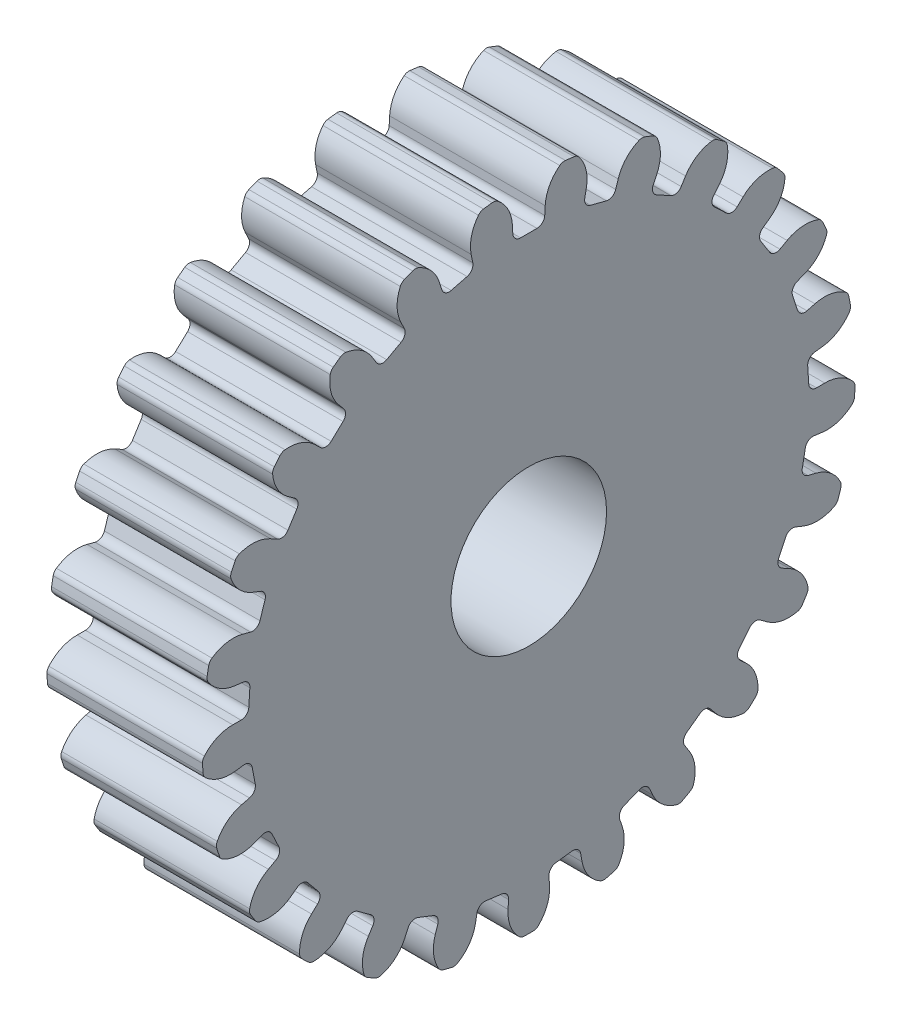
SolidWorks part; units mm, degrees
ref_plane "Plan de face" through (0, 0, 0) normal (0, 0, 1) x (1, 0, 0)
ref_plane "Plan de dessus" through (0, 0, 0) normal (0, 1, 0) x (1, 0, 0)
ref_plane "Plan de droite" through (0, 0, 0) normal (1, 0, 0) x (0, 0, -1)
sketch "Esquisse1" plane through (0, 0, 0) normal (1, 0, 0) x (0, 0, -1)
  circle A0 centre (0, 0) radius 10.5
  circle A1 centre (0, 0) radius 2.5
  dimension "D1" = 21
  dimension "D2" = 5
extrude "Extrusion1" add sketch "Esquisse1" along normal blind 5
sketch "Esquisse22" plane through (0, 0, 0) normal (-1, 0, 0) x (0, 0, 1)
  line L0 (0, 0) -> (0, 10.5) construction
  line L1 (-0.5, 9) -> (0.5, 9)
  line L2 (0.5, 9) -> (0.5278, 9.5)
  line L3 (0, 0) -> (-0.5, 9) construction
  line L4 (-0.5, 9) -> (-0.5278, 9.5)
  line L6 (-0.5278, 9.5) -> (0, 9.5) construction
  line L7 (-0.5278, 9.5) -> (-0.5824, 10.4838) construction
  circle A0 centre (0, 0) radius 10.5 construction
  arc A1 (-0.5278, 9.5) -> (-1.0824, 10.4441) centre (-1.7214, 9.4337) ccw
  arc A2 (-1.0824, 10.4441) -> (1.0824, 10.4441) centre (0, 0) cw
  arc A3 (0.5278, 9.5) -> (1.0824, 10.4441) centre (1.7214, 9.4337) cw
  point P13 (0, 9)
  dimension "D1" = 0.5
  dimension "D2" = 0.5
  dimension "D3" = 1.5
  dimension "D4" = 180
  dimension "D6" = 0.5
extrude "Enlèv. mat.-Extru.2" cut sketch "Esquisse22" against normal up to next (5 mm away)
fillet "Congé2" radius 0.25 4 edges at (2.5, 10.4441, 1.0824) (2.5, 9, 0.5) (2.5, 9, -0.5) (2.5, 10.4441, -1.0824)
pattern_circular "Répétition circulaire1" count 25 over 360 about axis through (0, 0, 0) along (1, 0, 0) of "Enlèv. mat.-Extru.2", "Congé2"
